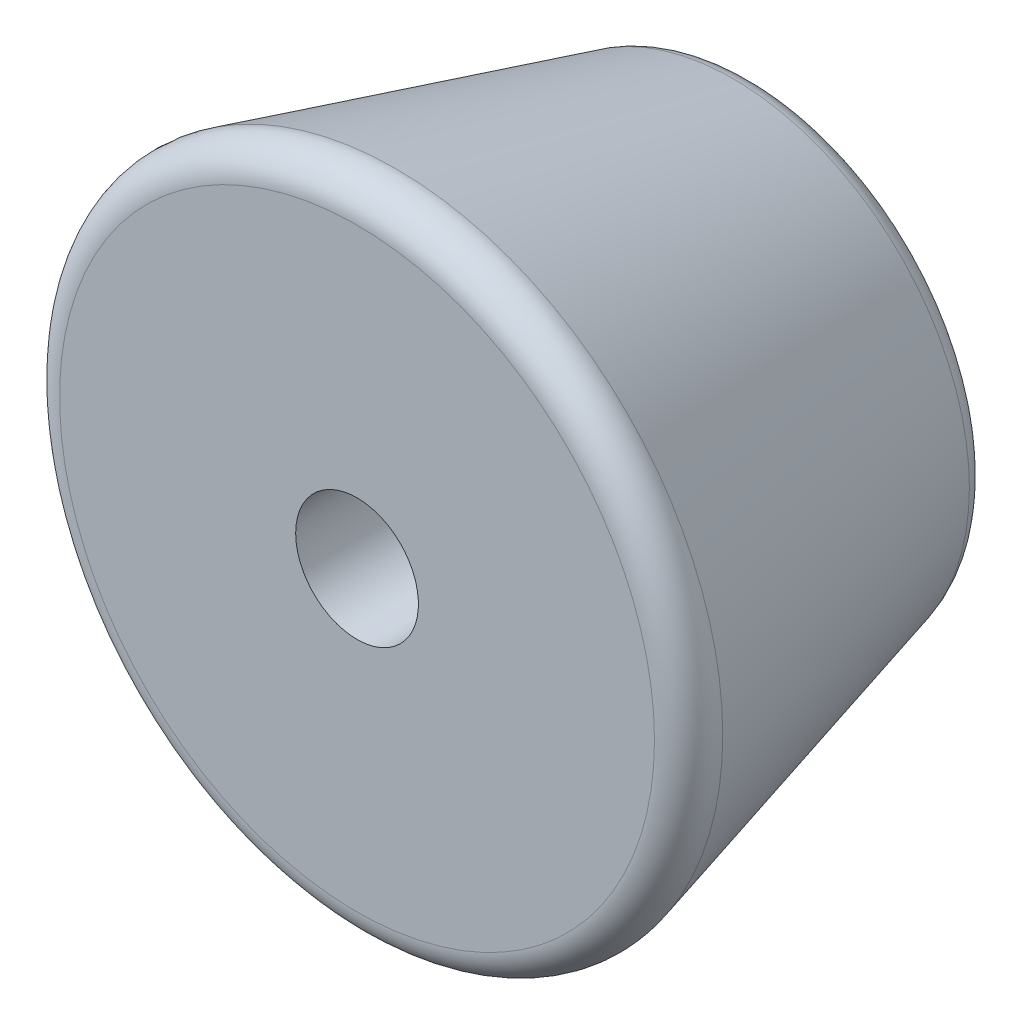
SolidWorks part; units mm, degrees
ref_plane "Front Plane" through (0, 0, 0) normal (0, 0, 1) x (1, 0, 0)
ref_plane "Top Plane" through (0, 0, 0) normal (0, 1, 0) x (1, 0, 0)
ref_plane "Right Plane" through (0, 0, 0) normal (1, 0, 0) x (0, 0, -1)
sketch "Sketch1" plane through (0, 0, 0) normal (0, 1, 0) x (1, 0, 0)
  line L0 (0, 0) -> (0, 13)
  line L1 (0, 13) -> (7.5, 13)
  line L2 (7.5, 13) -> (11, 0)
  line L3 (11, 0) -> (0, 0)
  dimension "D1" = 13
  dimension "D2" = 11
  dimension "D3" = 7.5
revolve "Revolve1" add sketch "Sketch1" angle 360 about L0
sketch "Sketch2" plane through (0, 0, -13) normal (0, 0, -1) x (-1, 0, 0)
  circle A0 centre (0, 0) radius 5
  dimension "D1" = 10
extrude "Cut-Extrude1" cut sketch "Sketch2" against normal blind 7
sketch "Sketch3" plane through (0, 0, -6) normal (0, 0, -1) x (-1, 0, 0)
  circle A0 centre (0, 0) radius 2
  dimension "D1" = 4
extrude "Cut-Extrude2" cut sketch "Sketch3" against normal through all
fillet "Fillet1" radius 1 3 edges at (7.5, 0, -13) (-5, 0, -13) (11, 0, 0)
